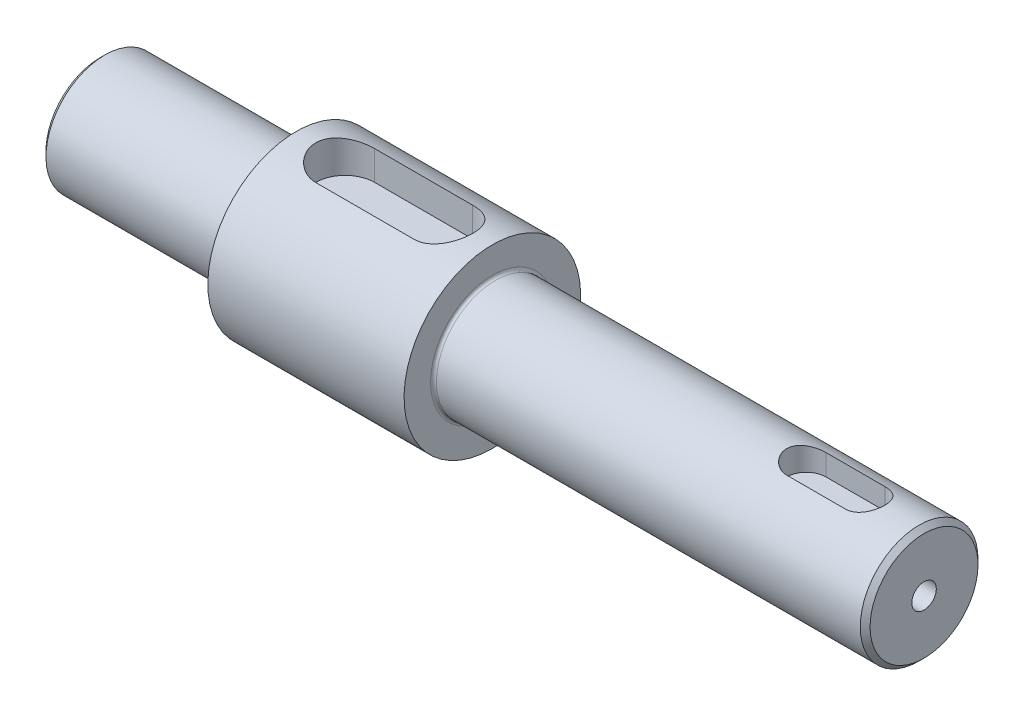
SolidWorks part; units mm, degrees
material "Alloy Steel (SS)"
ref_plane "Front Plane" through (0, 0, 0) normal (0, 0, 1) x (1, 0, 0)
ref_plane "Top Plane" through (0, 0, 0) normal (0, 1, 0) x (1, 0, 0)
ref_plane "Right Plane" through (0, 0, 0) normal (1, 0, 0) x (0, 0, -1)
sketch "Sketch3" plane through (0, 0, 0) normal (0, 0, 1) x (1, 0, 0)
  line L0 (0, 0) -> (0, 9) construction
  line L1 (-10, 9) -> (10, 9)
  line L2 (-10, 9) -> (-10, 6)
  line L3 (-10, 6) -> (-30, 6)
  line L4 (-30, 6) -> (-30, 0)
  line L5 (-30, 0) -> (0, 0) construction
  line L6 (10, 9) -> (10, 6)
  line L7 (10, 6) -> (32, 6)
  line L8 (60, 6) -> (60, 0)
  line L9 (60, 0) -> (0, 0) construction
  line L10 (-30, 0) -> (60, 0)
  line L14 (32, 6) -> (60, 6)
  point P6 (0, 9)
  dimension "D1" = 20
  dimension "D2" = 9
  dimension "D3" = 20
  dimension "D4" = 6
  dimension "D5" = 50
  dimension "D6" = 6
  dimension "D7" = 28
revolve "Revolve1" add sketch "Sketch3" angle 360 about L10
sketch "Sketch5" plane through (0, 0, 0) normal (0, 1, 0) x (1, 0, 0)
  line L0 (5, 0) -> (-5, 0) construction
  line L1 (5, -3) -> (-5, -3)
  line L2 (5, 3) -> (-5, 3)
  arc A0 (5, -3) -> (5, 3) centre (5, 0) ccw
  arc A1 (-5, 3) -> (-5, -3) centre (-5, 0) ccw
  point P2 (0, 0)
  dimension "D2" = 10
  dimension "D1" = 6
extrude "Cut-Extrude1" cut sketch "Sketch5" along normal blind 10 from offset 5.5
sketch "Sketch8" plane through (60, 0, 0) normal (1, 0, 0) x (0, 0, -1)
  circle A0 centre (0, 0) radius 6
  dimension "D1" = 12
extrude "Cut-Extrude4" cut sketch "Sketch8" against normal blind 6
sketch "Sketch9" plane through (0, 0, 0) normal (0, 1, 0) x (1, 0, 0)
  line L0 (0, 0) -> (54, 0) construction
  line L1 (54, -6) -> (54, 6) construction
  line L2 (42, 0) -> (48, 0) construction
  line L3 (42, 2) -> (48, 2)
  line L4 (42, -2) -> (48, -2)
  arc A0 (42, 2) -> (42, -2) centre (42, 0) ccw
  arc A1 (48, -2) -> (48, 2) centre (48, 0) ccw
  point P7 (45, 0)
  dimension "D1" = 4
  dimension "D2" = 6
  dimension "D3" = 9
extrude "Cut-Extrude5" cut sketch "Sketch9" against normal blind 2.5 from offset 6
fillet "Fillet1" radius 0.3 2 edges at (10, -6, 0) (-10, -6, 0)
chamfer "Chamfer1" distance 0.5 angle 45 2 edges at (54, 6, 0) (-30, -6, 0)
hole_wizard "M3 Tapped Hole1" positions "Sketch11" profile "Sketch12" tap size "M3" standard "ISO"
sketch "Sketch11" plane through (54, 0, 0) normal (1, 0, 0) x (0, 0, -1)
  point P0 (0, 0)
sketch "Sketch12" plane through (54, 0, 0) normal (0, 1, 0) x (0, 0, -1)
  line L0 (0, 0) -> (0, 7.5)
  line L1 (0, 7.5) -> (1.25, 6.7489)
  line L2 (1.25, 6.7489) -> (1.25, 0)
  line L5 (1.25, 0) -> (0, 0)
  line L10 (0, 7.5) -> (-1.25, 6.7489) construction
  line L11 (0, -6.35) -> (0, 107.95) construction
  dimension "Tap Drill Dia." = 2.5
  dimension "Tap Drill Depth" = 7.5
  dimension "Drill Angle" = 118
